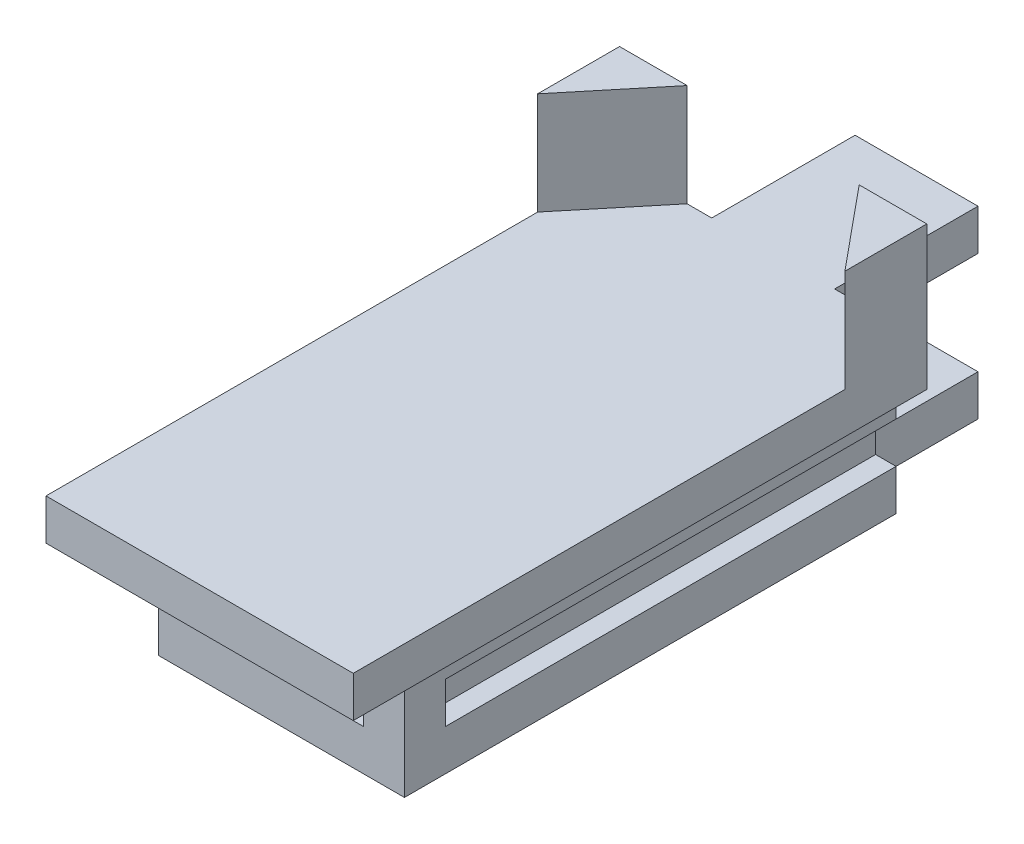
SolidWorks part; units mm, degrees
ref_plane "Front Plane" through (0, 0, 0) normal (0, 0, 1) x (1, 0, 0)
ref_plane "Top Plane" through (0, 0, 0) normal (0, 1, 0) x (1, 0, 0)
ref_plane "Right Plane" through (0, 0, 0) normal (1, 0, 0) x (0, 0, -1)
sketch "Sketch1" plane through (0, 0, 0) normal (0, 1, 0) x (1, 0, 0)
  line L1 (-3.75, -5) -> (3.75, -5)
  line L2 (-3.75, -5) -> (-3.75, 5)
  line L3 (-3.75, 5) -> (3.75, 5)
  line L4 (3.75, -5) -> (3.75, 5)
  line L5 (0, 5) -> (0, -5) construction
  line L6 (-3.75, 0) -> (3.75, 0) construction
  point P0 (0, 0)
  dimension "D1" = 10
  dimension "D2" = 7.5
extrude "Boss-Extrude1" add sketch "Sketch1" along normal blind 1
sketch "Sketch2" plane through (0, 1, 0) normal (0, 1, 0) x (1, 0, 0)
  line L0 (0, 5) -> (0, 3) construction
  line L1 (3.75, 5) -> (-3.75, 5) construction
  line L2 (-2.1, 5) -> (2.1, 5)
  line L3 (-2.1, 5) -> (-3.75, 3)
  line L4 (-3.75, 5) -> (-3.75, -5) construction
  line L5 (2.1, 5) -> (3.75, 3)
  line L6 (-3.75, 3) -> (-3.75, 5)
  line L7 (-3.75, 5) -> (-2.1, 5)
  line L8 (3.75, 3) -> (3.75, 5)
  line L9 (3.75, 5) -> (2.1, 5)
  point P8 (0, 5)
  line M2 (3.75, -5) -> (3.75, 5)
  line M3 (3.75, 5) -> (-3.75, 5)
  line M4 (-3.75, 5) -> (-3.75, -5)
  dimension "D1" = 2
extrude "Boss-Extrude2" add sketch "Sketch2" along normal blind 2.5 contours L3 M3 M4 | L5 M3 M2
ref_plane "Plane1" through (0, 3.5, 0) normal (0, 1, 0) x (1, 0, 0)
sketch "Sketch3" plane through (0, 3.5, 0) normal (0, 1, 0) x (1, 0, 0)
sketch "Sketch10" plane through (0, 0, 5) normal (0, 0, 1) x (1, 0, 0)
  line L1 (-3.75, 1) -> (3.75, 1)
  line L2 (-3.75, 1) -> (-3.75, 0)
  line L3 (-3.75, 0) -> (3.75, 0)
  line L4 (3.75, 1) -> (3.75, 0)
extrude "Boss-Extrude5" add sketch "Sketch10" along normal blind 2
sketch "Sketch56" plane through (0, 0, 7) normal (0, 0, 1) x (1, 0, 0)
  line L1 (-3.75, 1) -> (3.75, 1)
  line L2 (-3.75, 1) -> (-3.75, 0)
  line L3 (-3.75, 0) -> (3.75, 0)
  line L4 (3.75, 1) -> (3.75, 0)
extrude "Boss-Extrude17" add sketch "Sketch56" along normal blind 2
sketch "Sketch57" plane through (0, 0, -5) normal (0, 0, -1) x (-1, 0, 0)
  line L0 (0, 0) -> (0, 1) construction
  line L1 (-2.1, 1) -> (2.1, 1) construction
  line L3 (-1.5, 0) -> (1.5, 0)
  line L4 (-1.5, 0) -> (-1.5, 1)
  line L5 (-1.5, 1) -> (1.5, 1)
  line L6 (1.5, 0) -> (1.5, 1)
  line L7 (-1.5, 0) -> (1.5, 1) construction
  line L8 (-1.5, 1) -> (1.5, 0) construction
  point P5 (0, 0.5)
  dimension "D1" = 3
extrude "Boss-Extrude18" add sketch "Sketch57" along normal blind 5
sketch "Sketch58" plane through (1.5, 0, 0) normal (1, 0, 0) x (0, 0, -1)
  line L0 (10, 1) -> (5, 1) construction
  line L1 (10, 0) -> (8.5, 0)
  line L2 (10, 0) -> (10, 1)
  line L3 (10, 1) -> (8.5, 1)
  line L4 (8.5, 0) -> (8.5, 1)
  dimension "D1" = 1.5
extrude "Boss-Extrude19" add sketch "Sketch58" along normal blind 2
sketch "Sketch59" plane through (-1.5, 0, 0) normal (-1, 0, 0) x (0, 0, 1)
  line L0 (-10, 1) -> (-5, 1) construction
  line L1 (-10, 0) -> (-8.5, 0)
  line L2 (-10, 0) -> (-10, 1)
  line L3 (-10, 1) -> (-8.5, 1)
  line L4 (-8.5, 0) -> (-8.5, 1)
  dimension "D1" = 1.5
extrude "Boss-Extrude20" add sketch "Sketch59" along normal blind 2
sketch "Sketch60" plane through (0, 1, 0) normal (0, 1, 0) x (1, 0, 0)
  line L0 (3.5, 9.25) -> (2.5, 9.25) construction
  line L1 (3.5, 10) -> (3.5, 8.5) construction
  line L2 (3.5, 8.5) -> (1.5, 8.5) construction
  line L3 (2.5, 8.75) -> (2.5, 9.75)
  line L4 (0, 10) -> (0, 9.0116) construction
  line L5 (2.5, 8.5) -> (3.5, 8.5)
  line L6 (2.5, 8.5) -> (2.5, 10)
  line L7 (2.5, 10) -> (3.5, 10)
  line L8 (3.5, 8.5) -> (3.5, 10)
  line L9 (-3.5, 10) -> (3.5, 10) construction
  line L10 (2.5, 8.5) -> (3.5, 8.5)
  line L11 (2.5, 10) -> (3.5, 10)
  line L12 (-3.5, 9.25) -> (-2.5, 9.25) construction
  line L13 (-2.5, 10) -> (-3.5, 10)
  line L14 (-2.5, 8.5) -> (-3.5, 8.5)
  line L15 (-3.5, 8.5) -> (-3.5, 10)
  line L16 (-2.5, 10) -> (-3.5, 10)
  line L17 (-2.5, 8.5) -> (-2.5, 10)
  line L18 (-2.5, 8.5) -> (-3.5, 8.5)
  line L19 (-2.5, 8.75) -> (-2.5, 9.75)
  point P10 (2.5, 9.25)
  dimension "D1" = 1
extrude "Boss-Extrude23" add sketch "Sketch60" along normal blind 1.5 contours L8 L17 L6 L7 | L6 L4 L5 L3
sketch "Sketch61" plane through (0, 2.5, 0) normal (0, 1, 0) x (1, 0, 0)
  line L0 (2.5, 8.8704) -> (2.5, 9.6204)
  line L1 (-3.5, 10) -> (-3.5, 8.5) construction
  line L3 (-3.5, 8.8704) -> (-3.5, 9.6204)
  line L4 (-2.5, 8.5) -> (-2.5, 10) construction
  line L5 (-3.5, 8.8704) -> (-2.5, 8.8704)
  line L6 (-3.5, 8.8704) -> (-3.5, 9.6204)
  line L7 (-3.5, 9.6204) -> (-2.5, 9.6204)
  line L8 (-2.5, 8.8704) -> (-2.5, 9.6204)
  line L9 (0, 10) -> (0, 8.8704) construction
  line L10 (-2.5, 10) -> (2.5, 10) construction
  line L11 (3.5, 9.6204) -> (2.5, 9.6204)
  line L12 (3.5, 8.8704) -> (3.5, 9.6204)
  line L13 (3.5, 8.8704) -> (2.5, 8.8704)
  line L14 (3.5, 8.8704) -> (3.5, 9.6204)
  point P9 (-3.5, 9.2454)
  point P18 (3.5, 9.2454)
  line M3 (2.5, 10) -> (2.5, 8.5)
  line M5 (3.5, 8.5) -> (3.5, 10)
  dimension "D1" = 0.75
extrude "Cut-Extrude1" cut sketch "Sketch61" against normal blind 0.5 contours L5 L8 L7 L3 | L13 L11 M5 M3
sketch "Sketch62" plane through (0, 0, 0) normal (0, -1, 0) x (-1, 0, 0)
  line L0 (-1.5, 5) -> (1.5, 5)
  line L1 (0, 5) -> (0, -7) construction
  line L2 (3, -7) -> (-3, -7)
  line L3 (-3.75, 5) -> (-1.5, 5) construction
  line L4 (3, -7) -> (-3, -7)
  line L5 (3, -7) -> (3, 5)
  line L6 (3, 5) -> (-3, 5)
  line L7 (-3, -7) -> (-3, 5)
  point P10 (0, -7)
  line M5 (3.75, 5) -> (1.5, 5)
  line M13 (-1.5, 5) -> (-3.75, 5)
  dimension "D1" = 12
extrude "Boss-Extrude25" add sketch "Sketch62" along normal blind 3 contours L6 L1 L2 L5 M5 | L1 L0 L7 L4 M13
sketch "Sketch64" plane through (0, 0, 7) normal (0, 0, 1) x (1, 0, 0)
  line L0 (-2, 0) -> (2, 0)
  line L2 (-3.75, 0) -> (3.75, 0) construction
  line L4 (-2, 0) -> (2, 0)
  line L5 (-2, 0) -> (-2, -2)
  line L6 (-2, -2) -> (2, -2)
  line L7 (2, 0) -> (2, -2)
  point P7 (0, 0)
  line M2 (3, 0) -> (-3, 0)
  dimension "D1" = 2
extrude "Cut-Extrude2" cut sketch "Sketch64" against normal up to surface (12 mm away) contours L7 L5 L6 M2 up to face at (0.0375, 0.8281, -5)
sketch "Sketch65" plane through (0, 0, -5) normal (0, 0, -1) x (-1, 0, 0)
  line L0 (-3, -3) -> (3, -3) construction
  line L1 (-2, -2) -> (2, -2)
  line L2 (-2, -2) -> (-2, -3)
  line L3 (-2, -3) -> (2, -3)
  line L4 (2, -2) -> (2, -3)
  dimension "D1" = 4
extrude "Boss-Extrude26" add sketch "Sketch65" along normal blind 3
sketch "Sketch66" plane through (0, -3, 0) normal (0, -1, 0) x (-1, 0, 0)
  line L0 (0, -7) -> (0, -5) construction
  line L1 (0, -5) -> (0, 5) construction
  line L2 (3, -7) -> (-3, -7) construction
  circle A0 centre (0, -5) radius 1
  circle A1 centre (0, 5) radius 1
  dimension "D2" = 10
  dimension "D1" = 2
extrude "Cut-Extrude3" cut sketch "Sketch66" against normal up to surface (1 mm away) up to face at (0, -2, -2)
sketch "Sketch67" plane through (-3, 0, 0) normal (-1, 0, 0) x (0, 0, 1)
  line L0 (-5, 0) -> (-3, 0)
  line L1 (-5, 0) -> (9, 0) construction
  line L2 (-3, 0) -> (-3, -1)
  line L3 (-5, -3) -> (-5, 0) construction
  line L4 (-3, -1) -> (0, -1)
  line L5 (-3, -1) -> (-3, -2)
  line L6 (-3, -2) -> (0, -2)
  line L7 (0, -1) -> (0, -2)
  line L8 (-5, -1) -> (6, -1)
  line L9 (-5, -1) -> (-5, -2)
  line L10 (-5, -2) -> (6, -2)
  line L11 (6, -1) -> (6, -2)
  line M6 (-5, 0) -> (-5, -3)
  dimension "D1" = 2
  dimension "D2" = 1
  dimension "D3" = 1
  dimension "D4" = 3
  dimension "D5" = 11
sketch "Sketch68" plane through (3, 0, 0) normal (1, 0, 0) x (0, 0, -1)
  line L0 (5, 0) -> (3, 0)
  line L1 (-9, 0) -> (5, 0) construction
  line L2 (3, 0) -> (3, -1)
  line L3 (5, -3) -> (5, 0) construction
  line L4 (3, -1) -> (0, -1)
  line L5 (3, -1) -> (3, -2)
  line L6 (3, -2) -> (0, -2)
  line L7 (0, -1) -> (0, -2)
  line L8 (5, -2) -> (-6, -2)
  line L9 (5, -2) -> (5, -1)
  line L10 (5, -1) -> (-6, -1)
  line L11 (-6, -2) -> (-6, -1)
  line M8 (5, -3) -> (5, 0)
  dimension "D1" = 2
  dimension "D2" = 1
  dimension "D3" = 3
  dimension "D4" = 1
  dimension "D5" = 11
extrude "Cut-Extrude6" cut sketch "Sketch68" against normal blind 0.5 contours L11 L8 L7 L10 | L4 L7 L6 L5 | L10 L5 L8 M8
extrude "Cut-Extrude7" cut sketch "Sketch67" against normal blind 0.5 contours L11 L8 L7 L10 | L7 L4 L5 L6 | L10 L5 L8 M6
sketch "Sketch69" plane through (0, 0, 0) normal (0, -1, 0) x (1, 0, 0)
  line L0 (3.5, -8.5) -> (3.5, -10) construction
  line L1 (-3.5, -8.5) -> (3.5, -8.5)
  line L2 (-3.5, -8.5) -> (-3.5, -10)
  line L3 (-3.5, -10) -> (3.5, -10)
  line L4 (3.5, -8.5) -> (3.5, -10)
  line L5 (3.5, -10) -> (-3.5, -10) construction
extrude "Cut-Extrude8" cut sketch "Sketch69" against normal blind 10
